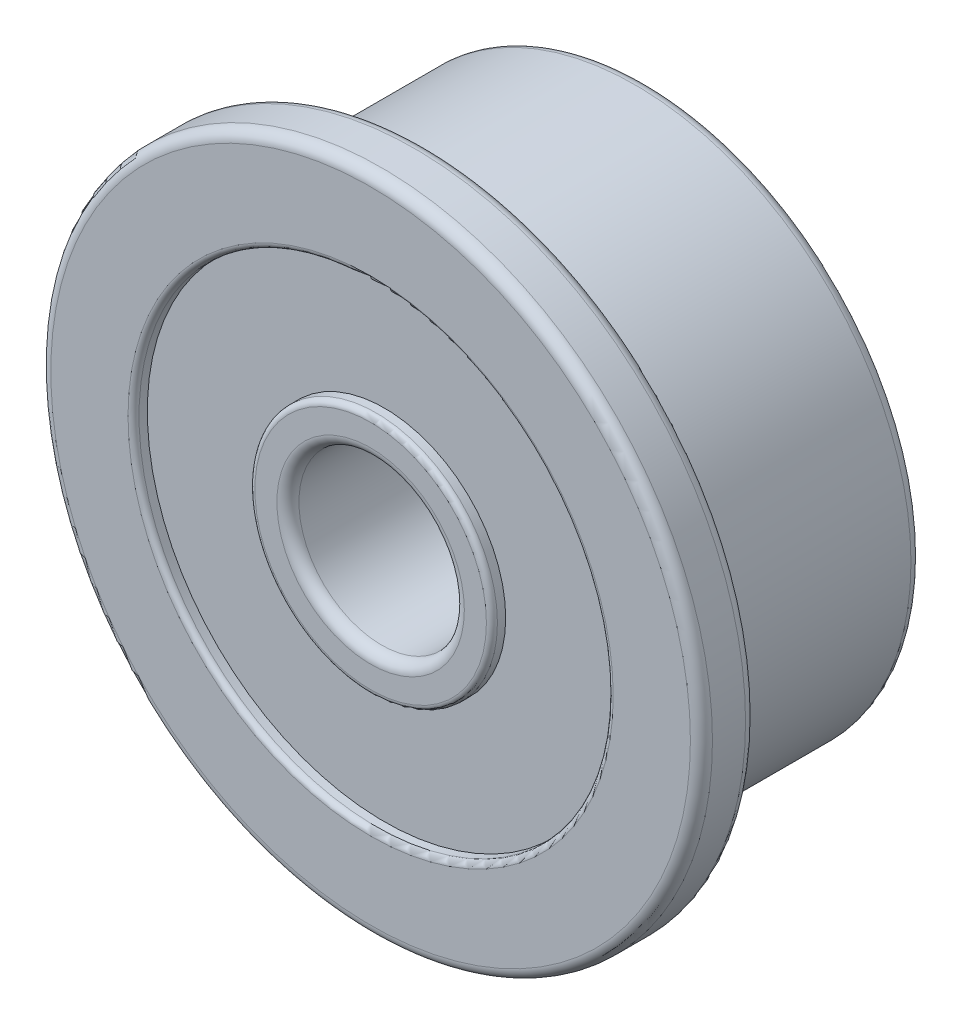
SolidWorks part; units mm, degrees
ref_plane "Front Plane" through (0, 0, 0) normal (0, 0, 1) x (1, 0, 0)
ref_plane "Top Plane" through (0, 0, 0) normal (0, 1, 0) x (1, 0, 0)
ref_plane "Right Plane" through (0, 0, 0) normal (1, 0, 0) x (0, 0, -1)
sketch "Sketch1" plane through (0, 0, 0) normal (0, 0, 1) x (1, 0, 0)
  circle A0 centre (0, 0) radius 1.5
  circle A1 centre (0, 0) radius 5
  dimension "D1" = 3
  dimension "D2" = 10
extrude "Boss-Extrude1" add sketch "Sketch1" along normal blind 4
sketch "Sketch2" plane through (0, 0, 4) normal (0, 0, 1) x (1, 0, 0)
  circle A0 centre (0, 0) radius 1.5 construction
  circle A1 centre (0, 0) radius 1.5
  circle A4 centre (0, 0) radius 6
  circle A5 centre (0, 0) radius 6
  dimension "D1" = 1
extrude "Boss-Extrude2" add sketch "Sketch2" along normal blind 1
fillet "Fillet1" radius 0.2 5 edges at (1.5, 0, 5) (1.5, 0, 0) (5, 0, 0) (6, 0, 5) (6, 0, 4)
sketch "Sketch3" plane through (0, 0, 0) normal (0, 0, -1) x (-1, 0, 0)
  circle A3 centre (0, 0) radius 2.2
  circle A4 centre (0, 0) radius 2.2
  circle A6 centre (0, 0) radius 4.3
  circle A7 centre (0, 0) radius 4.3
  dimension "D1" = 0.5
  dimension "D2" = 0.5
extrude "Cut-Extrude1" cut sketch "Sketch3" against normal blind 0.25
sketch "Sketch4" plane through (0, 0, 5) normal (0, 0, 1) x (1, 0, 0)
  circle A0 centre (0, 0) radius 2.2 construction
  circle A1 centre (0, 0) radius 4.3
  circle A2 centre (0, 0) radius 4.3
  circle A3 centre (0, 0) radius 2.2
  dimension "D1" = 0
extrude "Cut-Extrude2" cut sketch "Sketch4" against normal blind 0.25
fillet "Fillet2" radius 0.1 4 edges at (-4.3, 0, 0) (-2.2, 0, 0) (2.2, 0, 5) (4.3, 0, 5)
